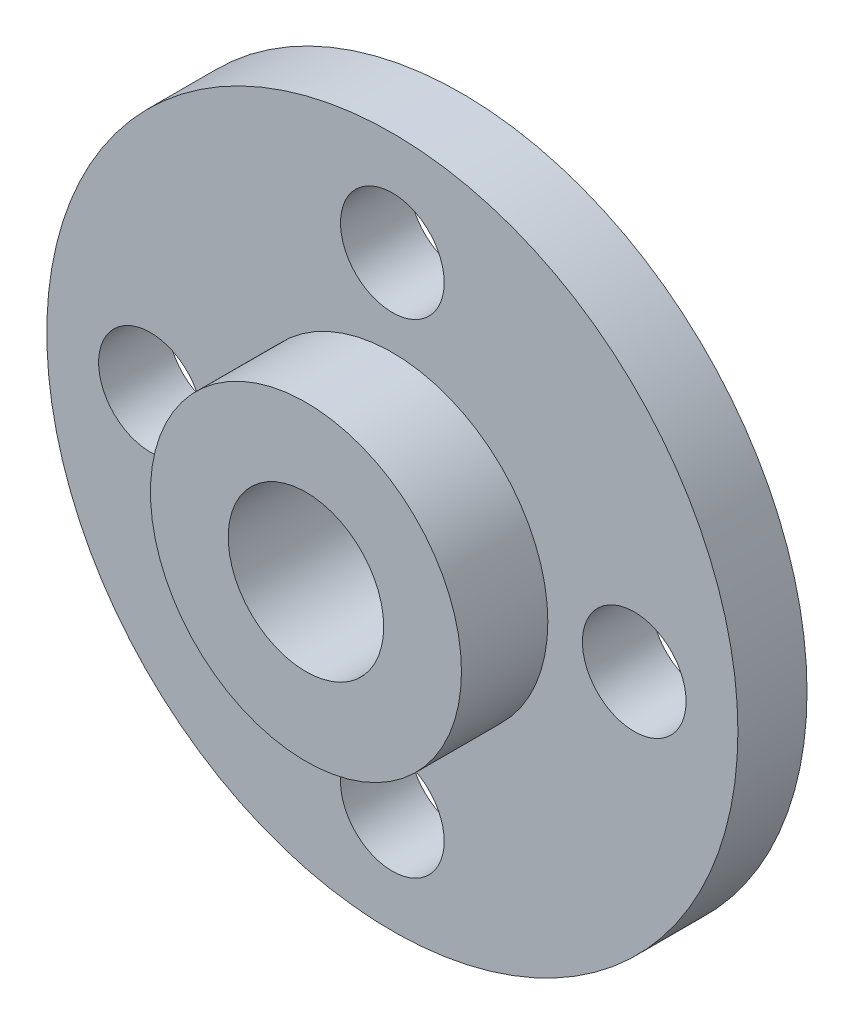
SolidWorks part; units mm, degrees
ref_plane "前视基准面" through (0, 0, 0) normal (0, 0, 1) x (1, 0, 0)
ref_plane "上视基准面" through (0, 0, 0) normal (0, 1, 0) x (1, 0, 0)
ref_plane "右视基准面" through (0, 0, 0) normal (1, 0, 0) x (0, 0, -1)
sketch "草图1" plane through (0, 0, 0) normal (0, 0, 1) x (1, 0, 0)
  circle A0 centre (0, 0) radius 10
  circle A1 centre (0, 0) radius 2.25
  circle A2 centre (7, 0) radius 1.5
  circle A3 centre (0, -7) radius 1.5
  circle A4 centre (-7, 0) radius 1.5
  circle A5 centre (0, 7) radius 1.5
  point P15 (0, 0)
  dimension "D1" = 7
  dimension "D2" = 4
extrude "凸台-拉伸1" add sketch "草图1" along normal blind 2
sketch "草图2" plane through (0, 0, 2) normal (0, 0, 1) x (1, 0, 0)
  circle A0 centre (0, 0) radius 2.25
  circle A1 centre (0, 0) radius 4.5
extrude "凸台-拉伸2" add sketch "草图2" along normal blind 2.5
